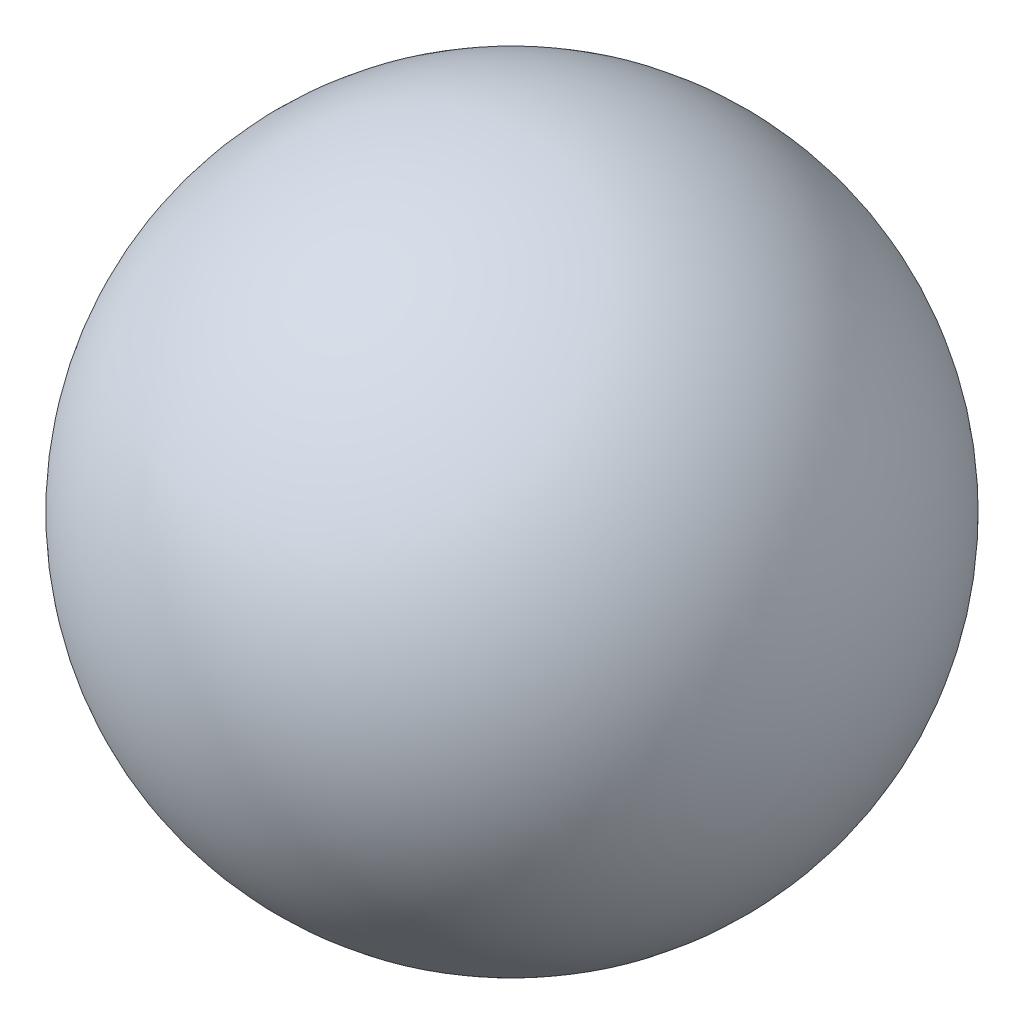
SolidWorks part; units mm, degrees
ref_plane "Front Plane" through (0, 0, 0) normal (0, 0, 1) x (1, 0, 0)
ref_plane "Top Plane" through (0, 0, 0) normal (0, 1, 0) x (1, 0, 0)
ref_plane "Right Plane" through (0, 0, 0) normal (1, 0, 0) x (0, 0, -1)
sketch "Sketch1" plane through (0, 0, 0) normal (0, 0, 1) x (1, 0, 0)
  line L0 (0, -9.5) -> (0, 9.5)
  arc A0 (0, -9.5) -> (0, 9.5) centre (0, 0) ccw
  dimension "D1" = 19
revolve "Revolve1" add sketch "Sketch1" angle 360 about L0
